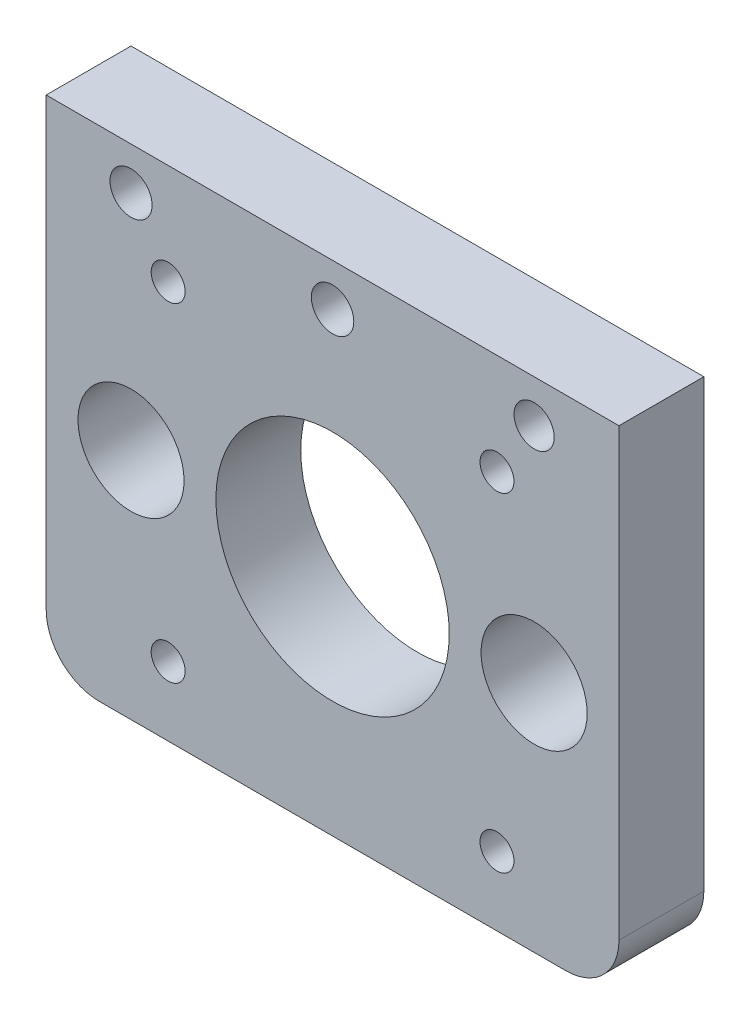
SolidWorks part; units mm, degrees
ref_plane "Front Plane" through (0, 0, 0) normal (0, 0, 1) x (1, 0, 0)
ref_plane "Top Plane" through (0, 0, 0) normal (0, 1, 0) x (1, 0, 0)
ref_plane "Right Plane" through (0, 0, 0) normal (1, 0, 0) x (0, 0, -1)
sketch "Sketch1" plane through (0, 0, 0) normal (0, 0, 1) x (1, 0, 0)
  line L0 (-27, 21) -> (27, 21) construction
  line L1 (-22, -22) -> (22, -22)
  line L2 (-27, -17) -> (-27, 25)
  line L3 (-27, 25) -> (27, 25)
  line L4 (27, -17) -> (27, 25)
  line L5 (0, -22) -> (0, 0) construction
  line L6 (-15.5, -15.5) -> (15.5, -15.5) construction
  line L7 (-15.5, -15.5) -> (-15.5, 15.5) construction
  line L8 (-15.5, 15.5) -> (15.5, 15.5) construction
  line L9 (15.5, -15.5) -> (15.5, 15.5) construction
  line L10 (-15.5, -15.5) -> (15.5, 15.5) construction
  line L11 (-15.5, 15.5) -> (15.5, -15.5) construction
  circle A0 centre (-19, 0) radius 5
  circle A1 centre (19, 0) radius 5
  circle A2 centre (0, 0) radius 11
  circle A3 centre (0, 21) radius 2
  circle A4 centre (-19, 21) radius 1.9846
  circle A5 centre (19, 21) radius 1.8944
  circle A6 centre (-15.5, 15.5) radius 1.6
  circle A7 centre (15.5, 15.5) radius 1.6
  circle A8 centre (15.5, -15.5) radius 1.6
  circle A9 centre (-15.5, -15.5) radius 1.6
  arc A10 (27, -17) -> (22, -22) centre (22, -17) cw
  arc A11 (-22, -22) -> (-27, -17) centre (-22, -17) cw
  point P4 (0, 0)
  point P31 (27, -22)
  point P34 (-27, -22)
  dimension "D1" = 19
  dimension "D4" = 25
  dimension "D7" = 31
  dimension "D8" = 5
  dimension "D2" = 38
  dimension "D3" = 54
  dimension "D5" = 22
  dimension "D6" = 4
  dimension "D9" = 31
extrude "Boss-Extrude1" add sketch "Sketch1" along normal blind 8
